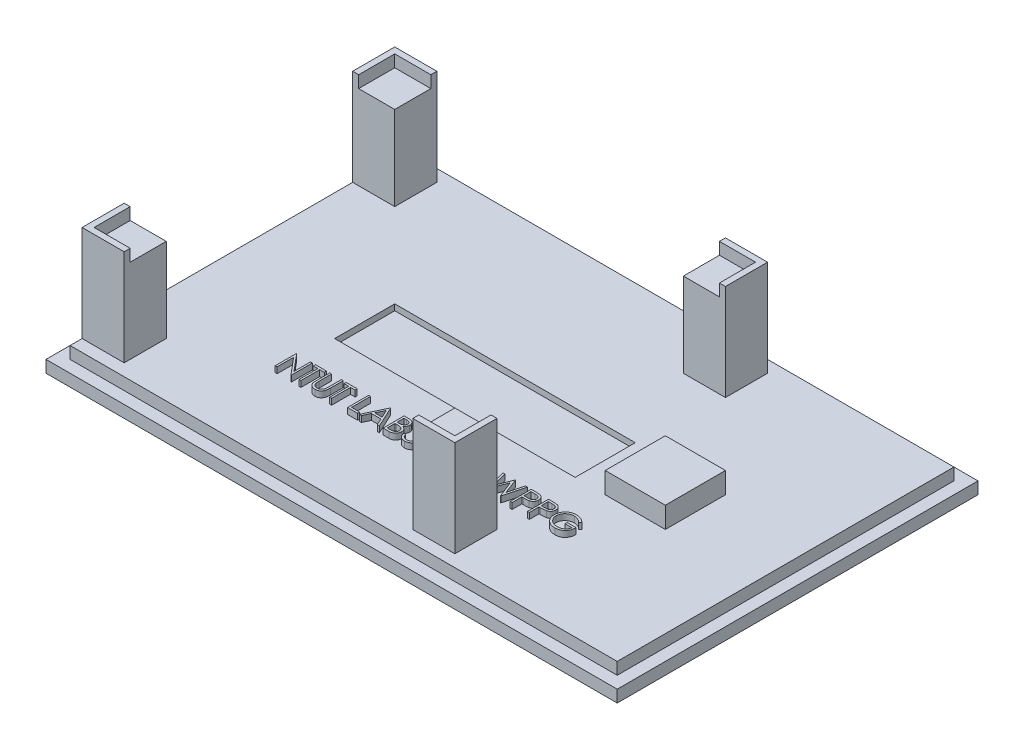
SolidWorks part; units mm, degrees
ref_plane "前基準面" through (0, 0, 0) normal (0, 0, 1) x (1, 0, 0)
ref_plane "上基準面" through (0, 0, 0) normal (0, 1, 0) x (1, 0, 0)
ref_plane "右基準面" through (0, 0, 0) normal (1, 0, 0) x (0, 0, -1)
sketch "草圖1" plane through (0, 0, 0) normal (0, 1, 0) x (1, 0, 0)
  line L1 (0, 0) -> (95, 0)
  line L2 (0, 0) -> (0, 60)
  line L3 (0, 60) -> (95, 60)
  line L4 (95, 0) -> (95, 60)
  dimension "D1" = 95
  dimension "D2" = 60
extrude "填料-伸長1" add sketch "草圖1" along normal blind 2
sketch "草圖2" plane through (0, 2, 0) normal (0, 1, 0) x (1, 0, 0)
  line L1 (2, 2) -> (93, 2)
  line L2 (2, 2) -> (2, 58)
  line L3 (2, 58) -> (93, 58)
  line L4 (93, 2) -> (93, 58)
  dimension "D1" = 91
  dimension "D2" = 56
extrude "填料-伸長2" add sketch "草圖2" along normal blind 2
sketch "草圖5" plane through (0, 4, 0) normal (0, 1, 0) x (1, 0, 0)
  line L1 (68, 35) -> (78, 35)
  line L2 (68, 35) -> (68, 25)
  line L3 (68, 25) -> (78, 25)
  line L4 (78, 35) -> (78, 25)
  dimension "D1" = 10
  dimension "D2" = 10
extrude "填料-伸長6" add sketch "草圖5" along normal blind 3.5
sketch "草圖14" plane through (0, 4, 0) normal (0, 1, 0) x (1, 0, 0)
sketch "草圖15" plane through (0, 4, 0) normal (0, 1, 0) x (1, 0, 0)
  line L0 (2, 11) -> (9, 11)
  line L1 (2, 56) -> (9, 56)
  line L2 (2, 56) -> (2, 49)
  line L3 (2, 49) -> (9, 49)
  line L4 (9, 56) -> (9, 49)
  line L5 (2, 11) -> (2, 4)
  line L6 (2, 4) -> (9, 4)
  line L7 (9, 11) -> (9, 4)
  line L12 (57, 56) -> (64, 56)
  line L13 (57, 56) -> (57, 49)
  line L14 (57, 49) -> (64, 49)
  line L15 (64, 56) -> (64, 49)
  line L16 (57, 11) -> (64, 11)
  line L17 (57, 11) -> (57, 4)
  line L18 (57, 4) -> (64, 4)
  line L19 (64, 11) -> (64, 4)
  dimension "D1" = 7
  dimension "D2" = 7
  dimension "D3" = 7
  dimension "D4" = 7
  dimension "D6" = 7
sketch "草圖16" plane through (0, 4, 0) normal (0, 1, 0) x (1, 0, 0)
sketch "草圖18" plane through (0, 4, 0) normal (0, 1, 0) x (1, 0, 0)
sketch "草圖24" plane through (0, 4, 0) normal (0, 1, 0) x (1, 0, 0)
extrude "填料-伸長7" add sketch "草圖15" along normal blind 16
sketch "草圖27" plane through (0, 20, 0) normal (0, 1, 0) x (1, 0, 0)
  line L1 (9, 49) -> (3, 49)
  line L2 (9, 49) -> (9, 55)
  line L3 (9, 55) -> (3, 55)
  line L4 (3, 49) -> (3, 55)
  line L5 (57, 49) -> (63, 49)
  line L6 (57, 49) -> (57, 55)
  line L7 (57, 55) -> (63, 55)
  line L8 (63, 49) -> (63, 55)
  line L9 (57, 11) -> (63, 11)
  line L10 (57, 11) -> (57, 5)
  line L11 (57, 5) -> (63, 5)
  line L12 (63, 11) -> (63, 5)
  line L13 (9, 11) -> (3, 11)
  line L14 (9, 11) -> (9, 5)
  line L15 (9, 5) -> (3, 5)
  line L16 (3, 11) -> (3, 5)
  dimension "D1" = 6
  dimension "D2" = 6
  dimension "D3" = 6
  dimension "D4" = 6
  dimension "D5" = 6
  dimension "D6" = 6
  dimension "D7" = 6
  dimension "D8" = 6
extrude "除料-伸長1" cut sketch "草圖27" against normal blind 2
sketch "草圖28" plane through (0, 4, 0) normal (0, 1, 0) x (1, 0, 0)
  line L1 (23, 25) -> (63, 25)
  line L2 (23, 25) -> (23, 35)
  line L3 (23, 35) -> (63, 35)
  line L4 (63, 25) -> (63, 35)
  dimension "D1" = 40
  dimension "D2" = 10
extrude "除料-伸長2" cut sketch "草圖28" against normal blind 1
sketch "草圖29" plane through (0, 4, 0) normal (0, 1, 0) x (1, 0, 0)
  text T0 "NTUT LAB321 MWPPG"
extrude "填料-伸長8" add sketch "草圖29" along normal blind 1
